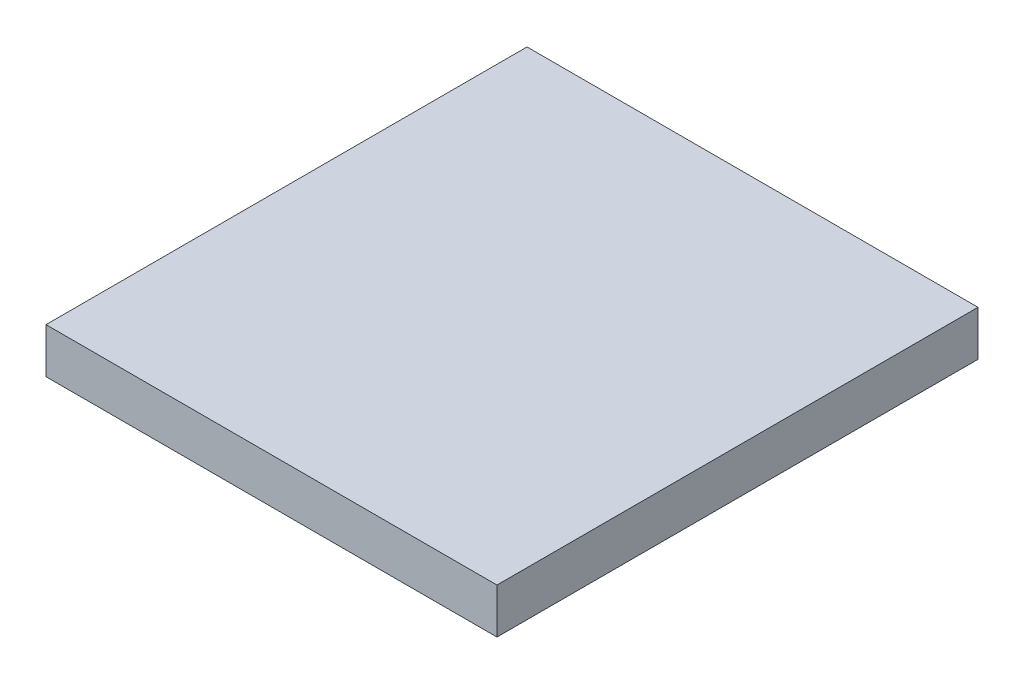
SolidWorks part; units mm, degrees
ref_plane "Front Plane" through (0, 0, 0) normal (0, 0, 1) x (1, 0, 0)
ref_plane "Top Plane" through (0, 0, 0) normal (0, 1, 0) x (1, 0, 0)
ref_plane "Right Plane" through (0, 0, 0) normal (1, 0, 0) x (0, 0, -1)
sketch "Sketch1" plane through (0, 0, 0) normal (0, 1, 0) x (1, 0, 0)
  line L1 (-45, 48) -> (45, 48)
  line L2 (-45, 48) -> (-45, -48)
  line L3 (-45, -48) -> (45, -48)
  line L4 (45, 48) -> (45, -48)
  dimension "D1" = 45
  dimension "D2" = 45
  dimension "D3" = 48
  dimension "D4" = 48
extrude "Boss-Extrude1" add sketch "Sketch1" along normal mid plane 9
